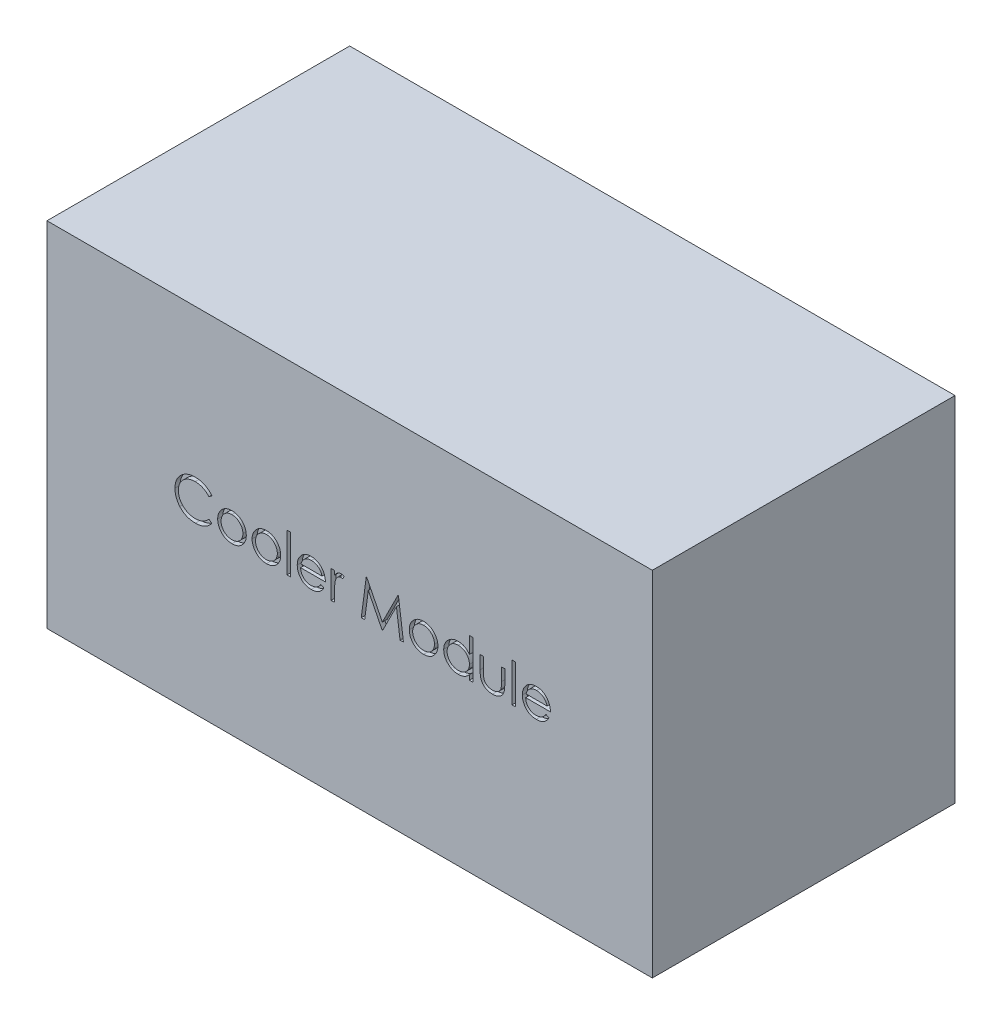
SolidWorks part; units mm, degrees
ref_plane "Front Plane" through (0, 0, 0) normal (0, 0, 1) x (1, 0, 0)
ref_plane "Top Plane" through (0, 0, 0) normal (0, 1, 0) x (1, 0, 0)
ref_plane "Right Plane" through (0, 0, 0) normal (1, 0, 0) x (0, 0, -1)
sketch "Sketch1" plane through (0, 0, 0) normal (0, 0, 1) x (1, 0, 0)
  line L1 (-152.4, -88.9) -> (152.4, -88.9)
  line L2 (-152.4, -88.9) -> (-152.4, 88.9)
  line L3 (-152.4, 88.9) -> (152.4, 88.9)
  line L4 (152.4, -88.9) -> (152.4, 88.9)
  line L5 (-152.4, -88.9) -> (152.4, 88.9) construction
  line L6 (-152.4, 88.9) -> (152.4, -88.9) construction
  point P0 (0, 0)
  dimension "D1" = 304.8
  dimension "D2" = 177.8
extrude "Boss-Extrude1" add sketch "Sketch1" along normal mid plane 152.4
sketch "Sketch2" plane through (0, 0, 76.2) normal (0, 0, 1) x (1, 0, 0)
  text T0 "Cooler Module" font "Century Gothic" height in points 72
extrude "Cut-Extrude1" cut sketch "Sketch2" against normal blind 2.54
